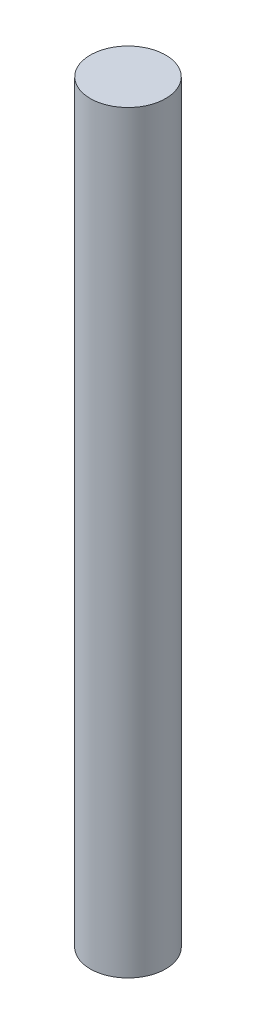
SolidWorks part; units mm, degrees
ref_plane "Alzado" through (0, 0, 0) normal (0, 0, 1) x (1, 0, 0)
ref_plane "Planta" through (0, 0, 0) normal (0, 1, 0) x (1, 0, 0)
ref_plane "Vista lateral" through (0, 0, 0) normal (1, 0, 0) x (0, 0, -1)
sketch "Croquis1" plane through (0, 0, 0) normal (0, 1, 0) x (1, 0, 0)
  circle A0 centre (0, 0) radius 4
  dimension "D1" = 8
extrude "Saliente-Extruir1" add sketch "Croquis1" along normal blind 80
